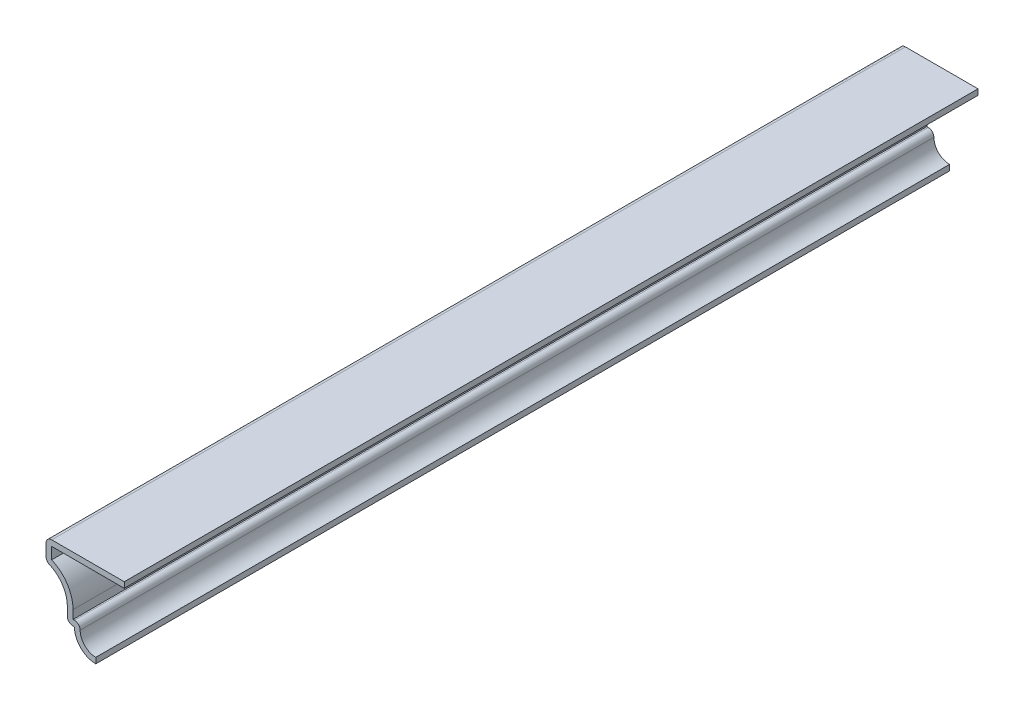
SolidWorks part; units mm, degrees
ref_plane "Front Plane" through (0, 0, 0) normal (0, 0, 1) x (1, 0, 0)
ref_plane "Top Plane" through (0, 0, 0) normal (0, 1, 0) x (1, 0, 0)
ref_plane "Right Plane" through (0, 0, 0) normal (1, 0, 0) x (0, 0, -1)
sketch "Sketch1" plane through (0, 0, 0) normal (0, 0, 1) x (1, 0, 0)
  line L0 (6.35, 19.05) -> (-11.1125, 19.05)
  line L1 (-11.1125, 19.05) -> (-11.1125, 14.2875)
  line L2 (-6.35, 4.7625) -> (-4.7625, 4.7625)
  line L3 (-6.35, 4.7625) -> (-6.35, 7.9375)
  arc A0 (-11.1125, 14.2875) -> (-6.35, 7.9375) centre (-12.9646, 7.9375) cw
  arc A1 (-4.7625, 4.7625) -> (0, 0) centre (0, 4.7625) ccw
  point P10 (-6.35, 9.8315)
  point P11 (0, 0)
  point P12 (0, 0)
  point P13 (-6.35, 6.716)
  point P14 (-6.35, 7.6345)
  dimension "D7" = 3.175
  dimension "D1" = 17.4625
  dimension "D2" = 19.05
  dimension "D3" = 6.35
  dimension "D4" = 4.7625
  dimension "D5" = 9.525
  dimension "D6" = 4.7625
extrude "Extrude-Thin1" add sketch "Sketch1" against normal blind 190.5 thin thin type one direction reverse wall 1.27
fillet "Fillet1" radius 1.27 4 edges at (-3.2534, 6.0325, -95.25) (-11.1125, 19.05, -95.25) (-6.35, 4.7625, -95.25) (-11.1125, 14.2875, -95.25)
